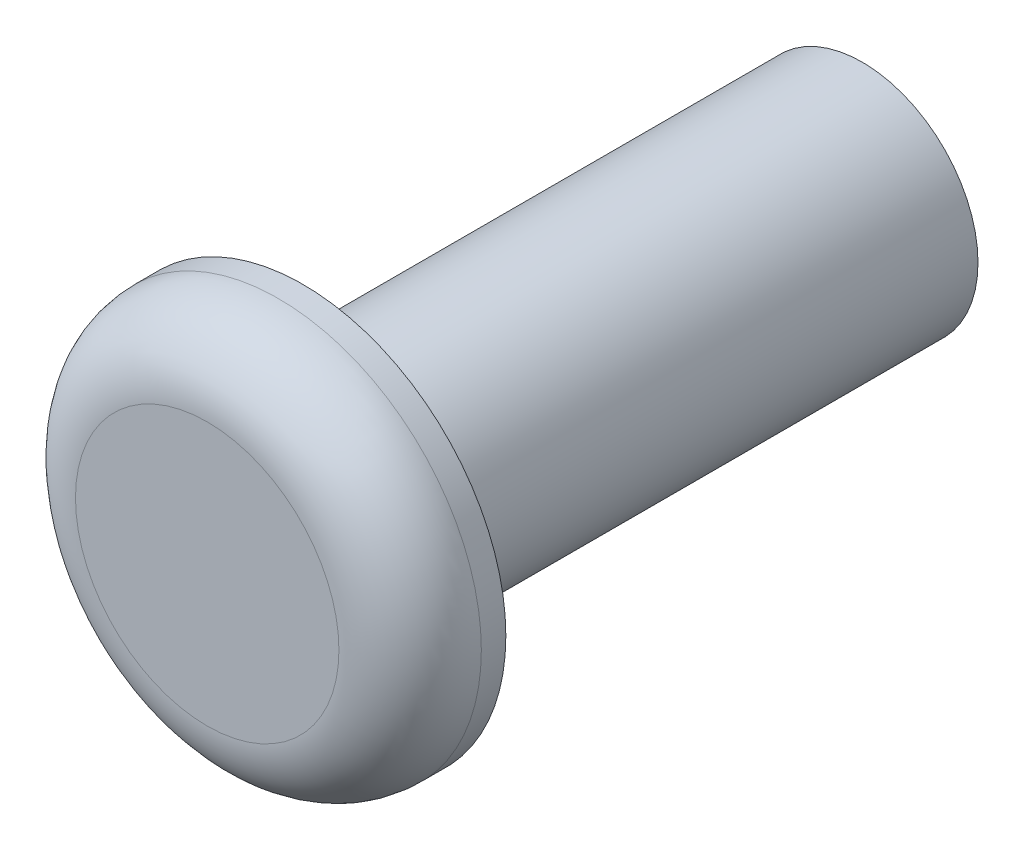
SolidWorks part; units mm, degrees
ref_plane "Front Plane" through (0, 0, 0) normal (0, 0, 1) x (1, 0, 0)
ref_plane "Top Plane" through (0, 0, 0) normal (0, 1, 0) x (1, 0, 0)
ref_plane "Right Plane" through (0, 0, 0) normal (1, 0, 0) x (0, 0, -1)
sketch "Sketch1" plane through (0, 0, 0) normal (1, 0, 0) x (0, 0, -1)
  line L0 (-43.0288, 0) -> (43.1806, 0) construction
  line L1 (0, 0) -> (0, 0.9398)
  line L2 (0.508, 1.4478) -> (0.6829, 1.4478)
  line L3 (0.6829, 1.4478) -> (0.6829, 0.8255)
  line L4 (0.6829, 0.8255) -> (4.6736, 0.8255)
  line L5 (4.6736, 0.8255) -> (4.6736, 0)
  line L6 (4.6736, 0) -> (0, 0)
  arc A0 (0, 0.9398) -> (0.508, 1.4478) centre (0.508, 0.9398) cw
  point P11 (0, 1.4478)
  dimension "D4" = 0.508
  dimension "D1" = 4.6736
  dimension "D2" = 1.4478
  dimension "D3" = 0.8255
revolve "Revolve1" add sketch "Sketch1" angle 360 about L0
